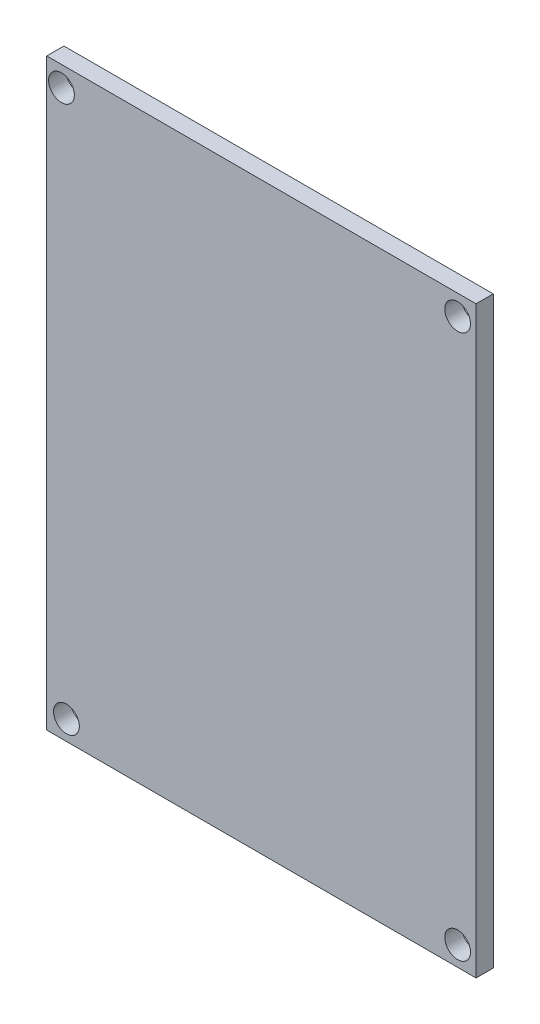
SolidWorks part; units mm, degrees
ref_plane "Front Plane" through (0, 0, 0) normal (0, 0, 1) x (1, 0, 0)
ref_plane "Top Plane" through (0, 0, 0) normal (0, 1, 0) x (1, 0, 0)
ref_plane "Right Plane" through (0, 0, 0) normal (1, 0, 0) x (0, 0, -1)
sketch "Sketch1" plane through (0, 0, 0) normal (0, 0, 1) x (1, 0, 0)
  line L1 (25, 34) -> (-25, 34)
  line L2 (25, 34) -> (25, -34)
  line L3 (25, -34) -> (-25, -34)
  line L4 (-25, 34) -> (-25, -34)
  line L5 (25, 34) -> (-25, -34) construction
  line L6 (25, -34) -> (-25, 34) construction
  point P0 (0, 0)
  dimension "D1" = 50
  dimension "D2" = 68
extrude "Boss-Extrude1" add sketch "Sketch1" along normal blind 2
sketch "Sketch2" plane through (0, 0, 0) normal (0, 0, -1) x (-1, 0, 0)
  circle A0 centre (23.2858, 31.6513) radius 1.5
  circle A1 centre (-22.8512, 31.6513) radius 1.5
  circle A2 centre (-22.8512, -31.7237) radius 1.5
  circle A3 centre (22.7064, -31.7237) radius 1.5
  dimension "D1" = 3
  dimension "D2" = 3
  dimension "D3" = 3
  dimension "D4" = 3
extrude "Cut-Extrude1" cut sketch "Sketch2" against normal blind 2
